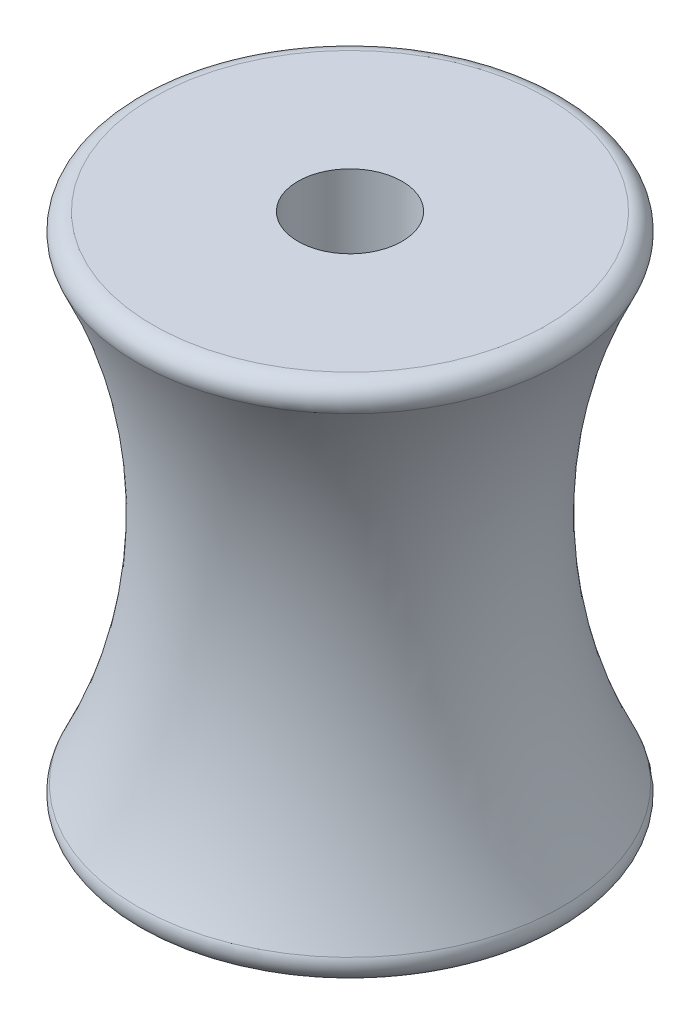
SolidWorks part; units mm, degrees
ref_plane "Plan de face" through (0, 0, 0) normal (0, 0, 1) x (1, 0, 0)
ref_plane "Plan de dessus" through (0, 0, 0) normal (0, 1, 0) x (1, 0, 0)
ref_plane "Plan de droite" through (0, 0, 0) normal (1, 0, 0) x (0, 0, -1)
sketch "Esquisse1" plane through (0, 0, 0) normal (0, 0, 1) x (1, 0, 0)
  line L0 (0, 0) -> (0, 30) construction
  line L1 (-3, 30) -> (-3, 0)
  line L2 (-3, 30) -> (-13, 30)
  line L3 (-3, 0) -> (-13, 0)
  line L4 (-3, 0) -> (0, 0) construction
  arc A0 (-13, 30) -> (-13, 0) centre (-40, 15) cw
  dimension "D1" = 30
  dimension "D2" = 3
  dimension "D3" = 10
  dimension "D4" = 10
  dimension "D5" = 30
  dimension "D6" = 40
revolve "Révolution1" add sketch "Esquisse1" angle 360 about L0
fillet "Congé1" radius 1 2 edges at (0, 0, -13) (0, 30, -13)
